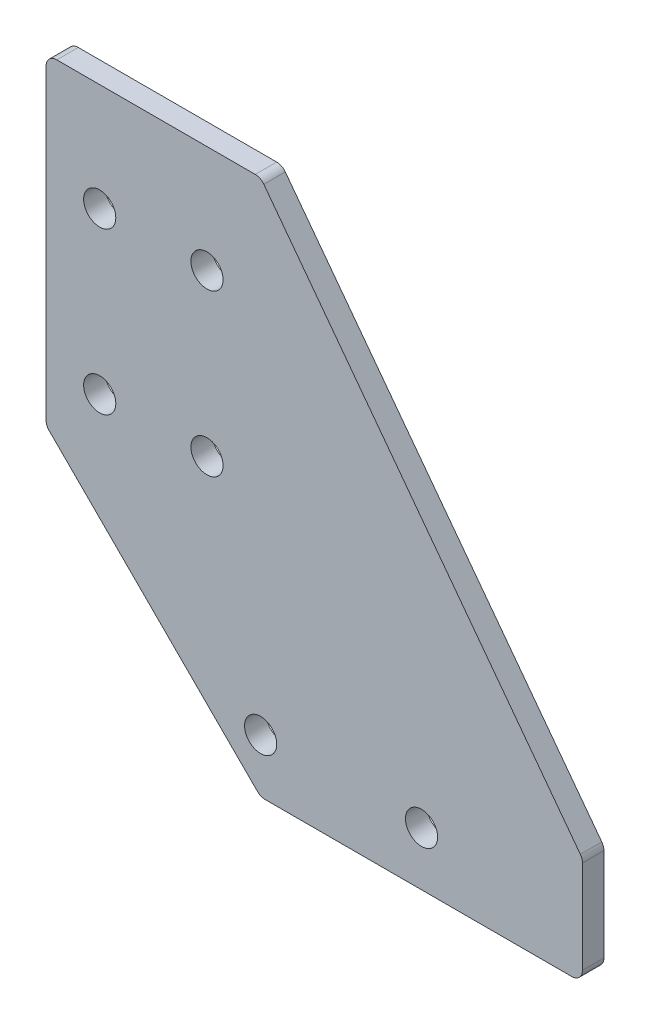
SolidWorks part; units mm, degrees
material "环氧板3240"
ref_plane "前视基准面" through (0, 0, 0) normal (0, 0, 1) x (1, 0, 0)
ref_plane "上视基准面" through (0, 0, 0) normal (0, 1, 0) x (1, 0, 0)
ref_plane "右视基准面" through (0, 0, 0) normal (1, 0, 0) x (0, 0, -1)
other "Configuration Table"
sketch "草图1" plane through (0, 0, 0) normal (0, 0, 1) x (1, 0, 0)
  line L0 (-5, 45) -> (15, 45)
  line L1 (15, 45) -> (45, 5)
  line L2 (45, 5) -> (45, -5)
  line L3 (45, -5) -> (15, -5)
  line L4 (15, -5) -> (-5, 15)
  line L5 (-5, 15) -> (-5, 45)
  line L6 (0, 45) -> (0, 0) construction
  line L7 (0, 0) -> (45, 0) construction
  line L9 (10, 45) -> (10, 0) construction
  line L10 (0, 35) -> (10, 35) construction
  line L11 (0, 20) -> (10, 20) construction
  circle A0 centre (0, 35) radius 1.5
  circle A1 centre (30, 0) radius 1.5
  circle A2 centre (0, 20) radius 1.5
  circle A3 centre (15, 0) radius 1.5
  circle A4 centre (10, 35) radius 1.5
  circle A5 centre (10, 20) radius 1.5
  dimension "D8" = 3
  dimension "D9" = 25
  dimension "D10" = 15
  dimension "D2" = 15
  dimension "D11" = 20
  dimension "D12" = 5.5711
  dimension "D1" = 10
  dimension "D3" = 20
  dimension "D4" = 30
  dimension "D5" = 50
  dimension "D6" = 20
  dimension "D7" = 20
  dimension "D13" = 5
  dimension "D14" = 10
  dimension "D15" = 53.13
extrude "凸台-拉伸1" add sketch "草图1" along normal blind 2 contours L1 L2 L3 L4 L5 L0
fillet "圆角1" radius 1 6 edges at (45, 5, 1) (45, -5, 1) (15, -5, 1) (-5, 15, 1) (15, 45, 1) (-5, 45, 1)
